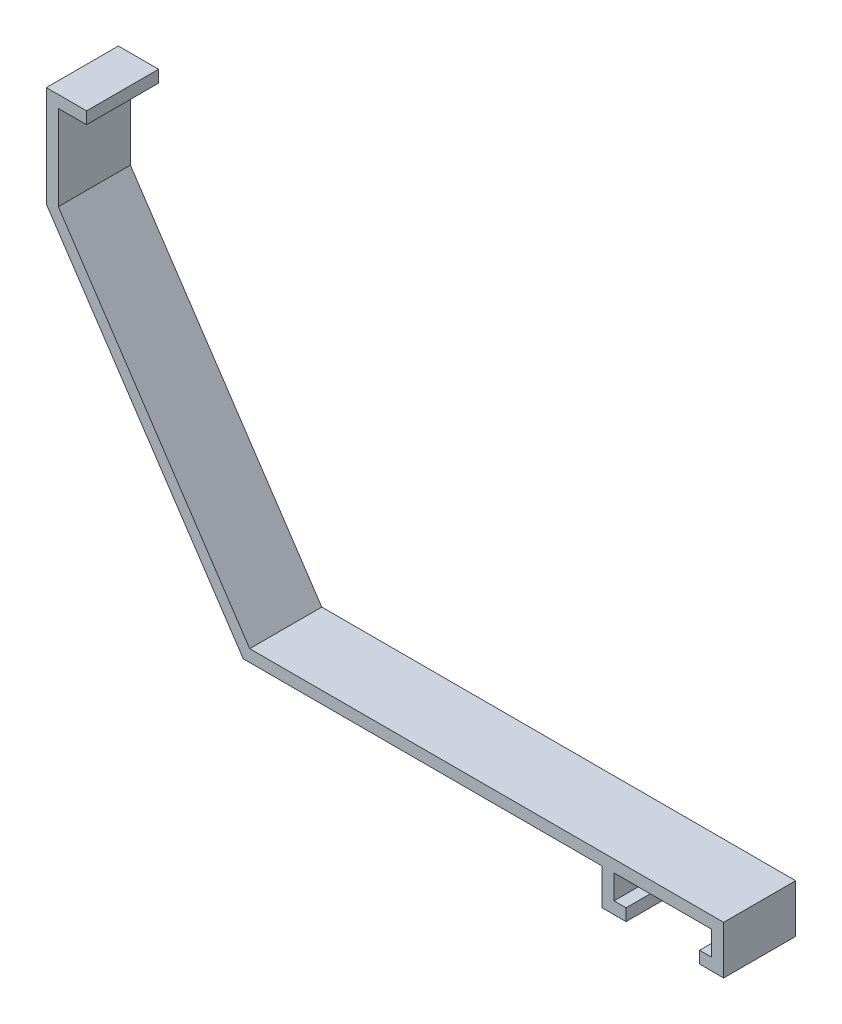
SolidWorks part; units mm, degrees
ref_plane "Front Plane" through (0, 0, 0) normal (0, 0, 1) x (1, 0, 0)
ref_plane "Top Plane" through (0, 0, 0) normal (0, 1, 0) x (1, 0, 0)
ref_plane "Right Plane" through (0, 0, 0) normal (1, 0, 0) x (0, 0, -1)
sketch "Sketch1" plane through (0, 0, 0) normal (0, 0, 1) x (1, 0, 0)
  line L0 (0, 0) -> (-5.3213, 0)
  line L1 (-5.3213, 0) -> (-5.3213, -13.3192)
  line L2 (-5.3213, -13.3192) -> (20.7153, -52.3741)
  line L3 (20.7153, -52.3741) -> (68.1403, -52.3741)
  line L4 (68.1403, -52.3741) -> (68.1403, -57.1616)
  line L5 (68.1403, -57.1616) -> (71.3153, -57.1616)
  line L6 (71.3153, -57.1616) -> (71.3153, -55.5741)
  line L7 (71.3153, -55.5741) -> (69.7278, -55.5741)
  line L8 (69.7278, -55.5741) -> (69.7278, -52.3741)
  line L9 (69.7278, -52.3741) -> (82.6278, -52.3741)
  line L10 (82.6278, -52.3741) -> (82.6278, -55.5741)
  line L11 (82.6278, -55.5741) -> (81.0403, -55.5741)
  line L12 (81.0403, -55.5741) -> (81.0403, -57.1616)
  line L13 (81.0403, -57.1616) -> (84.2153, -57.1616)
  line L14 (84.2153, -57.1616) -> (84.2153, -50.7866)
  line L15 (84.2153, -50.7866) -> (21.5649, -50.7866)
  line L16 (21.5649, -50.7866) -> (-3.7338, -12.8385)
  line L17 (-3.7338, -12.8385) -> (-3.7338, -1.5875)
  line L18 (-3.7338, -1.5875) -> (0, -1.5875)
  line L19 (0, -1.5875) -> (0, 0)
  dimension "D1" = 1.5875
  dimension "D2" = 1.5875
  dimension "D3" = 1.5875
  dimension "D4" = 1.5875
  dimension "D5" = 1.5875
  dimension "D6" = 123.69
  dimension "D7" = 63.5
  dimension "D8" = 11.251
  dimension "D9" = 45.6079
  dimension "D10" = 3.7338
  dimension "D11" = 3.2
  dimension "D12" = 12.9
extrude "Boss-Extrude1" add sketch "Sketch1" along normal blind 9.525
